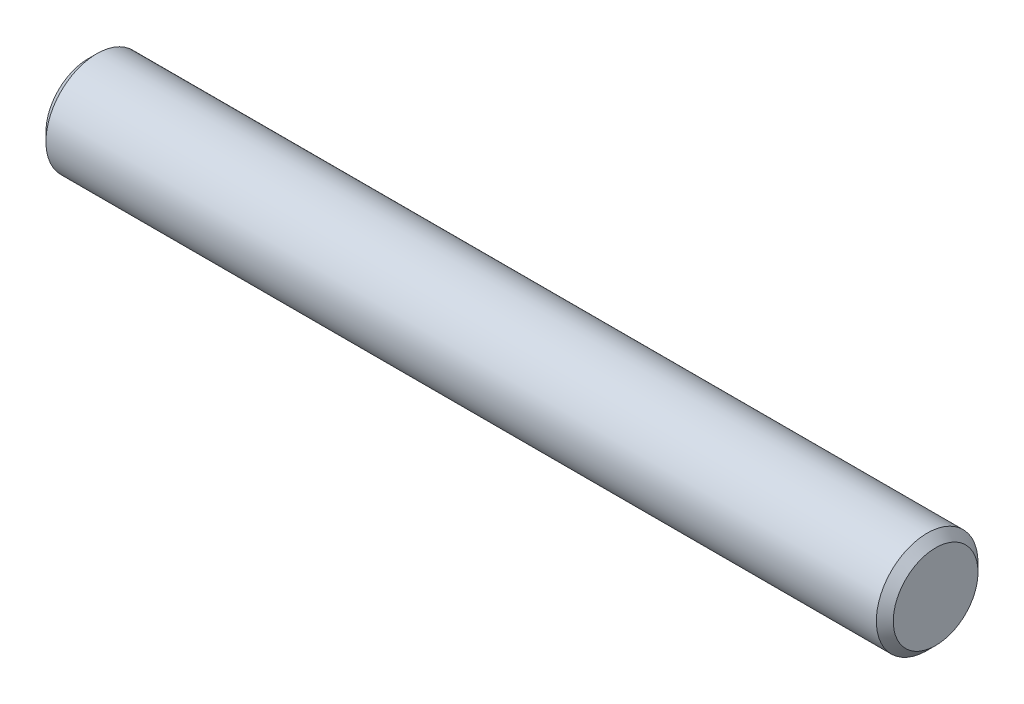
SolidWorks part; units mm, degrees
ref_plane "Front Plane" through (0, 0, 0) normal (0, 0, 1) x (1, 0, 0)
ref_plane "Top Plane" through (0, 0, 0) normal (0, 1, 0) x (1, 0, 0)
ref_plane "Right Plane" through (0, 0, 0) normal (1, 0, 0) x (0, 0, -1)
sketch "Sketch1" plane through (0, 0, 0) normal (1, 0, 0) x (0, 0, -1)
  circle A0 centre (0, 0) radius 3
  dimension "D1" = 6
extrude "Extrude1" add sketch "Sketch1" along normal blind 50
chamfer "Chamfer1" distance 0.5 angle 45 2 edges at (0, 0, -3) (50, 0, -3)
